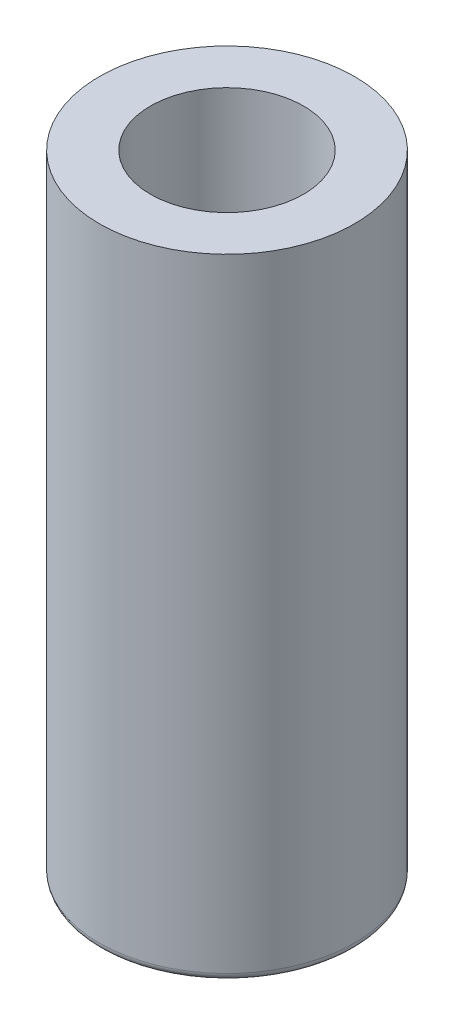
SolidWorks part; units mm, degrees
material "1.0037 (S235JR)"
ref_plane "Front Plane" through (0, 0, 0) normal (0, 0, 1) x (1, 0, 0)
ref_plane "Top Plane" through (0, 0, 0) normal (0, 1, 0) x (1, 0, 0)
ref_plane "Right Plane" through (0, 0, 0) normal (1, 0, 0) x (0, 0, -1)
sketch "Sketch1" plane through (0, 0, 0) normal (0, 1, 0) x (1, 0, 0)
  circle A0 centre (0, 0) radius 8.5
  dimension "D1" = 17
extrude "Boss-Extrude1" add sketch "Sketch1" along normal blind 42
hole_wizard "M12 Tapped Hole1" positions "3DSketch2" profile "Sketch2" tap size "M12" standard "ISO"
sketch3d "3DSketch2"
  point P4 (0, 0, 0)
  point P6 (0, 42, 0)
  point P9 (0, 0, 0)
  point P10 (0, 45, 0)
sketch "Sketch2" plane through (0, 42, 0) normal (1, 0, 0) x (0, 0, 1)
  line L0 (0, 0) -> (0, 30.0644)
  line L1 (0, 30.0644) -> (5.1, 27)
  line L2 (5.1, 27) -> (5.1, 0)
  line L5 (5.1, 0) -> (0, 0)
  line L10 (0, 30.0644) -> (-5.1, 27) construction
  line L11 (0, -6.35) -> (0, 107.95) construction
  dimension "Tap Drill Dia." = 10.2
  dimension "Tap Drill Depth" = 27
  dimension "Drill Angle" = 118
cosmetic thread "Hole Thread3"
fillet "Fillet1" radius 0.5 1 edges at (0, 0, 8.5)
